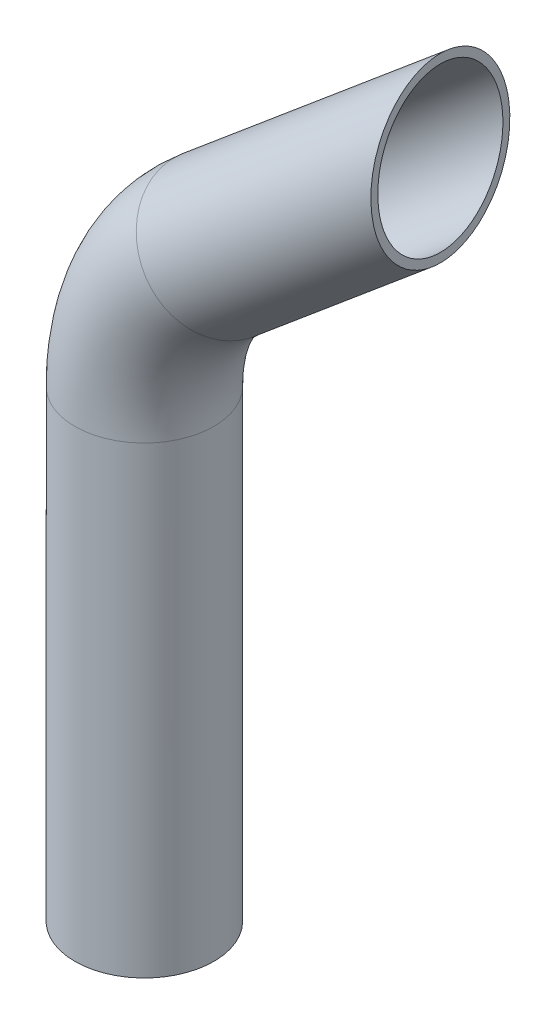
SolidWorks part; units mm, degrees
ref_plane "Front Plane" through (0, 0, 0) normal (0, 0, 1) x (1, 0, 0)
ref_plane "Top Plane" through (0, 0, 0) normal (0, 1, 0) x (1, 0, 0)
ref_plane "Right Plane" through (0, 0, 0) normal (1, 0, 0) x (0, 0, -1)
sketch "Sketch1" plane through (0, 0, 0) normal (0, 0, 1) x (1, 0, 0)
  line L0 (0, 0) -> (0, 200)
  line L1 (32.1491, 268.944) -> (147.0558, 365.3621)
  arc A0 (0, 200) -> (32.1491, 268.944) centre (90, 200) cw
  dimension "D2" = 90
  dimension "D1" = 200
  dimension "D3" = 150
  dimension "D4" = 130
sketch "Sketch3" plane through (0, 0, 0) normal (0, 1, 0) x (1, 0, 0)
  circle A0 centre (0, 0) radius 30
  dimension "D1" = 60
sweep "Sweep-Thin1" add profiles "Sketch3" path "Sketch1" parameters "D1"=3
sketch "Sketch4" plane through (0, 0, 0) normal (0, 0, 1) x (1, 0, 0)
  line L0 (127.7722, 388.3435) -> (127.7722, 310.019)
  line L1 (51.4327, 245.9627) -> (166.3394, 342.3808) construction
  line L2 (127.7722, 388.3435) -> (166.3394, 342.3808)
  line L3 (166.3394, 342.3808) -> (127.7722, 310.019)
extrude "Cut-Extrude1" cut sketch "Sketch4" against normal through all both and the other way through all
